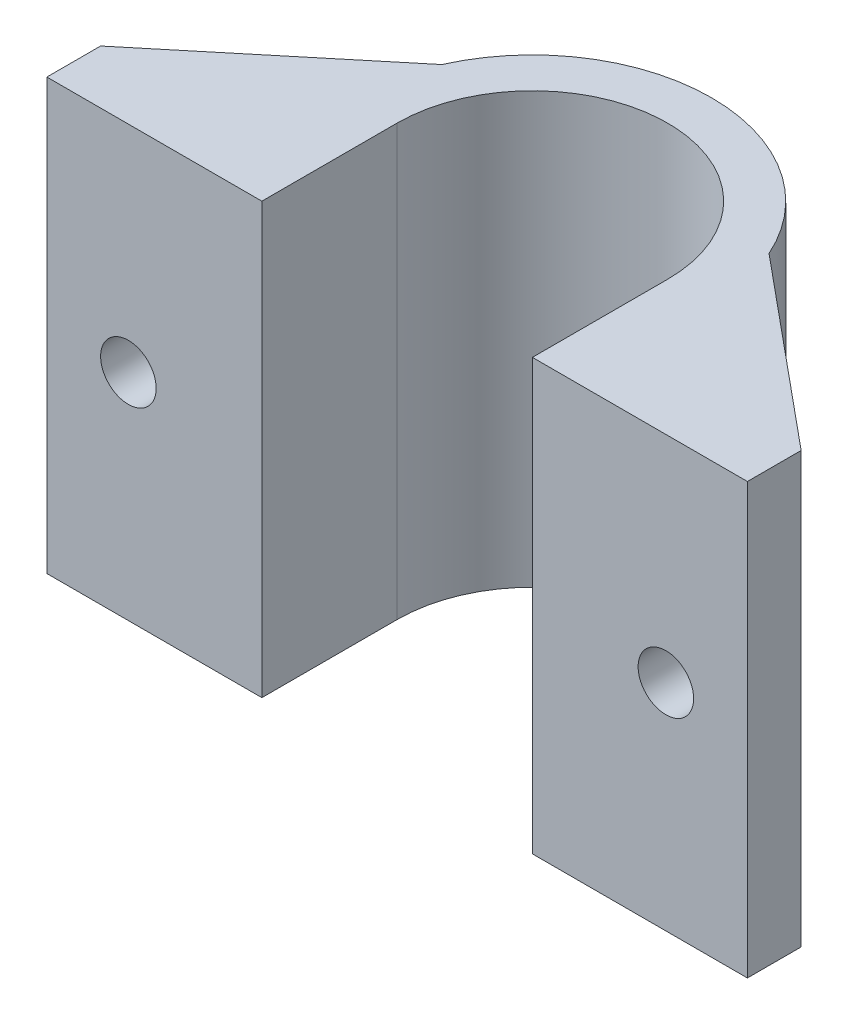
SolidWorks part; units mm, degrees
ref_plane "Alzado" through (0, 0, 0) normal (0, 0, 1) x (1, 0, 0)
ref_plane "Planta" through (0, 0, 0) normal (0, 1, 0) x (1, 0, 0)
ref_plane "Vista lateral" through (0, 0, 0) normal (1, 0, 0) x (0, 0, -1)
sketch "Croquis2" plane through (0, 0, 0) normal (0, 1, 0) x (1, 0, 0)
  line L0 (-7.55, 0) -> (-7.55, -7.55)
  line L1 (-7.55, -7.55) -> (-19.55, -7.55)
  line L2 (7.55, 0) -> (7.55, -7.55)
  line L3 (7.55, -7.55) -> (19.55, -7.55)
  line L4 (-19.55, -7.55) -> (-19.55, -4.55)
  line L5 (-19.55, -4.55) -> (-9.1318, 4.0757)
  line L6 (19.55, -7.55) -> (19.55, -4.55)
  line L7 (19.55, -4.55) -> (9.1318, 4.0757)
  arc A0 (7.55, 0) -> (-7.55, 0) centre (0, 0) ccw
  arc A1 (9.1318, 4.0757) -> (-9.1318, 4.0757) centre (0, 0) ccw
  dimension "D1" = 15.1
  dimension "D2" = 20
  dimension "D3" = 7.55
  dimension "D4" = 12
  dimension "D5" = 12
  dimension "D6" = 3
  dimension "D7" = 3
  dimension "D8" = 13.5256
  dimension "D9" = 13.5256
extrude "Saliente-Extruir1" add sketch "Croquis2" along normal blind 24
sketch "Croquis3" plane through (0, 0, 7.55) normal (0, 0, 1) x (1, 0, 0)
  line L0 (-7.55, 0) -> (7.55, 0) construction
  line L1 (7.55, 24) -> (-7.55, 24) construction
  line L2 (7.55, 24) -> (7.55, 0) construction
  line L3 (-7.55, 0) -> (7.55, 0) construction
  line L4 (7.55, 24) -> (-7.55, 24) construction
  line L5 (7.55, 24) -> (7.55, 0) construction
  line L6 (0, 24) -> (0, 0) construction
  line L8 (-7.55, 24) -> (-7.55, 0) construction
  line L9 (7.55, 12) -> (-7.55, 12) construction
  line L10 (0, 12) -> (15, 12) construction
  line L11 (0, 12) -> (-15, 12) construction
  circle A0 centre (15, 12) radius 1.55
  circle A1 centre (-15, 12) radius 1.55
  dimension "D2" = 3.1
  dimension "D4" = 3.1
  dimension "D1" = 15
  dimension "D3" = 15
extrude "Cortar-Extruir1" cut sketch "Croquis3" against normal through all
ref_plane "Plano1" through (0, 21, 0) normal (0, 1, 0) x (1, 0, 0)
sketch "Croquis4" plane through (0, 21, 0) normal (0, 1, 0) x (1, 0, 0)
  line L0 (-9.1318, 4.0757) -> (-19.55, -4.55) construction
  line L1 (-9.1318, 4.0757) -> (-19.55, -4.55)
  line L2 (-19.55, -4.55) -> (-9.1318, -4.55)
  line L3 (-9.1318, -4.55) -> (-9.1318, 4.0757)
extrude "Cortar-Extruir2" cut sketch "Croquis4" against normal blind 17
sketch "Croquis5" plane through (0, 21, 0) normal (0, 1, 0) x (1, 0, 0)
  line L0 (19.55, -4.55) -> (9.1318, 4.0757) construction
  line L1 (19.55, -4.55) -> (9.1318, 4.0757)
  line L2 (9.1318, 4.0757) -> (9.1318, -4.55)
  line L3 (9.1318, -4.55) -> (19.55, -4.55)
extrude "Cortar-Extruir3" cut sketch "Croquis5" against normal blind 17
